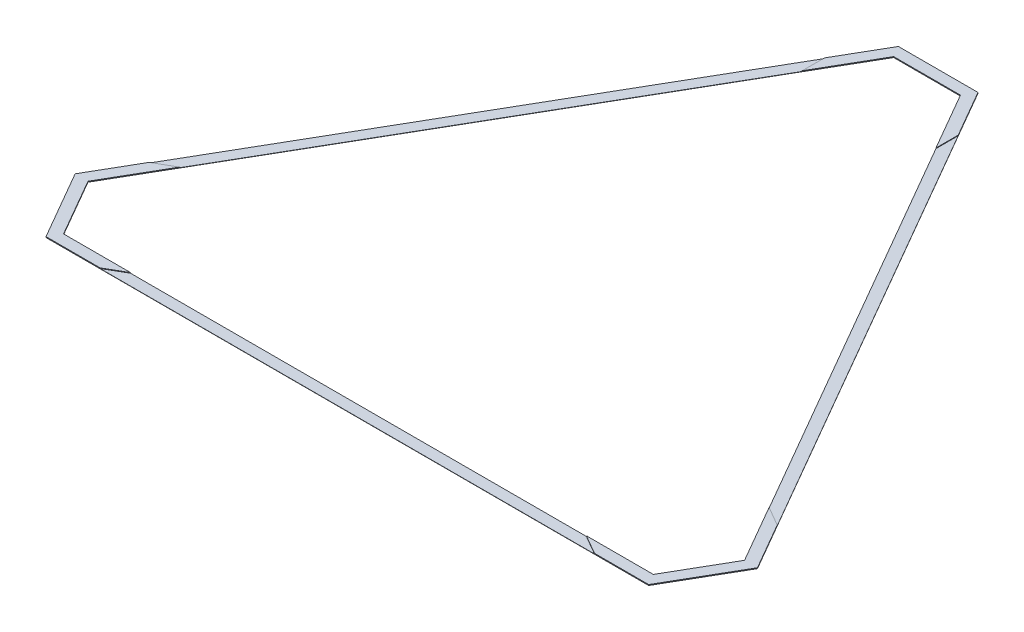
SolidWorks part; units mm, degrees
ref_plane "Front Plane" through (0, 0, 0) normal (0, 0, 1) x (1, 0, 0)
ref_plane "Top Plane" through (0, 0, 0) normal (0, 1, 0) x (1, 0, 0)
ref_plane "Right Plane" through (0, 0, 0) normal (1, 0, 0) x (0, 0, -1)
sketch "Sketch1" plane through (0, 0, 0) normal (0, 1, 0) x (1, 0, 0)
  line L0 (-152.4, 1642.446) -> (-1498.6, -689.2408)
  line L1 (-1498.6, -689.2408) -> (-1346.2, -953.2053)
  line L2 (-1346.2, -953.2053) -> (1346.2, -953.2053)
  line L3 (1346.2, -953.2053) -> (1498.6, -689.2408)
  line L4 (1498.6, -689.2408) -> (152.4, 1642.446)
  line L5 (152.4, 1642.446) -> (-152.4, 1642.446)
  line L6 (0, 0) -> (0, -953.2053) construction
  line L7 (0, 0) -> (825.5, 476.6026) construction
  line L8 (0, 0) -> (-825.5, 476.6026) construction
  line L9 (-181.7294, 1693.246) -> (-1557.2588, -689.2408)
  line L10 (-1557.2588, -689.2408) -> (-1375.5294, -1004.0053)
  line L11 (-1375.5294, -1004.0053) -> (1375.5294, -1004.0053)
  line L12 (1375.5294, -1004.0053) -> (1557.2588, -689.2408)
  line L13 (1557.2588, -689.2408) -> (181.7294, 1693.246)
  line L14 (181.7294, 1693.246) -> (-181.7294, 1693.246)
  dimension "D1" = 304.8
  dimension "D2" = 2692.4
  dimension "D3" = 50.8
extrude "Boss-Extrude1" add sketch "Sketch1" along normal blind 1.27 contours L13 L14 L9 L10 L11 L12 L5 L4 L3 L2 L1 L0
sketch "Sketch2" plane through (0, 1.27, 0) normal (0, 1, 0) x (1, 0, 0)
  line L0 (-305.308, 1479.2016) -> (-305.308, 1377.6016)
  line L1 (-181.7294, 1693.246) -> (-1557.2588, -689.2408) construction
  line L2 (-152.4, 1642.446) -> (-1498.6, -689.2408) construction
  line L3 (305.308, 1479.2016) -> (305.308, 1377.6016)
  line L4 (1557.2588, -689.2408) -> (181.7294, 1693.246) construction
  line L5 (1498.6, -689.2408) -> (152.4, 1642.446) construction
  line L6 (1375.5294, -1004.0053) -> (1557.2588, -689.2408) construction
  line L7 (1346.2, -953.2053) -> (1498.6, -689.2408) construction
  line L10 (-1375.5294, -1004.0053) -> (1375.5294, -1004.0053) construction
  line L11 (-1346.2, -953.2053) -> (1346.2, -953.2053) construction
  line L12 (-1498.6, -689.2408) -> (-1346.2, -953.2053) construction
  line L13 (-1557.2588, -689.2408) -> (-1375.5294, -1004.0053) construction
  line L14 (181.7294, 1693.246) -> (-181.7294, 1693.246) construction
  line L15 (152.4, 1642.446) -> (-152.4, 1642.446) construction
  line L16 (1375.5294, -1004.0053) -> (1557.2588, -689.2408)
  line L17 (1346.2, -953.2053) -> (1498.6, -689.2408)
  line L18 (-1375.5294, -1004.0053) -> (1375.5294, -1004.0053)
  line L19 (-1346.2, -953.2053) -> (1346.2, -953.2053)
  line L20 (-1498.6, -689.2408) -> (-1346.2, -953.2053)
  line L21 (-1557.2588, -689.2408) -> (-1375.5294, -1004.0053)
  line L22 (-181.7294, 1693.246) -> (-1557.2588, -689.2408)
  line L23 (181.7294, 1693.246) -> (-181.7294, 1693.246)
  line L24 (1557.2588, -689.2408) -> (181.7294, 1693.246)
  line L25 (1498.6, -689.2408) -> (152.4, 1642.446)
  line L26 (152.4, 1642.446) -> (-152.4, 1642.446)
  line L27 (-152.4, 1642.446) -> (-1498.6, -689.2408)
  line L28 (1433.6802, -475.1963) -> (1345.692, -424.3963)
  line L29 (1128.3722, -1004.0053) -> (1040.384, -953.2053)
  line L30 (-1128.3722, -1004.0053) -> (-1040.384, -953.2053)
  line L31 (-1433.6802, -475.1963) -> (-1345.692, -424.3963)
  point P24 (0, 0)
  line M15 (-152.4, 1642.446) -> (152.4, 1642.446)
  line M16 (152.4, 1642.446) -> (1498.6, -689.2408)
  line M17 (1498.6, -689.2408) -> (1346.2, -953.2053)
  line M18 (1346.2, -953.2053) -> (-1346.2, -953.2053)
  line M19 (-1346.2, -953.2053) -> (-1498.6, -689.2408)
  line M20 (-1498.6, -689.2408) -> (-152.4, 1642.446)
  line M21 (1557.2588, -689.2408) -> (181.7294, 1693.246)
  line M22 (181.7294, 1693.246) -> (-181.7294, 1693.246)
  line M23 (-181.7294, 1693.246) -> (-1557.2588, -689.2408)
  line M24 (-1557.2588, -689.2408) -> (-1375.5294, -1004.0053)
  line M25 (-1375.5294, -1004.0053) -> (1375.5294, -1004.0053)
  line M26 (1375.5294, -1004.0053) -> (1557.2588, -689.2408)
  dimension "D1" = 610.616
  dimension "D2" = 3
extrude "Boss-Extrude2" add sketch "Sketch2" along normal blind 2.6568 contours L3 L0 M21 M22 M23 M20 M15 M16 | L29 L18 L28 L25 M26 M21 M17 M18 | L31 L22 L30 M24 M25 M18 M19 M20
